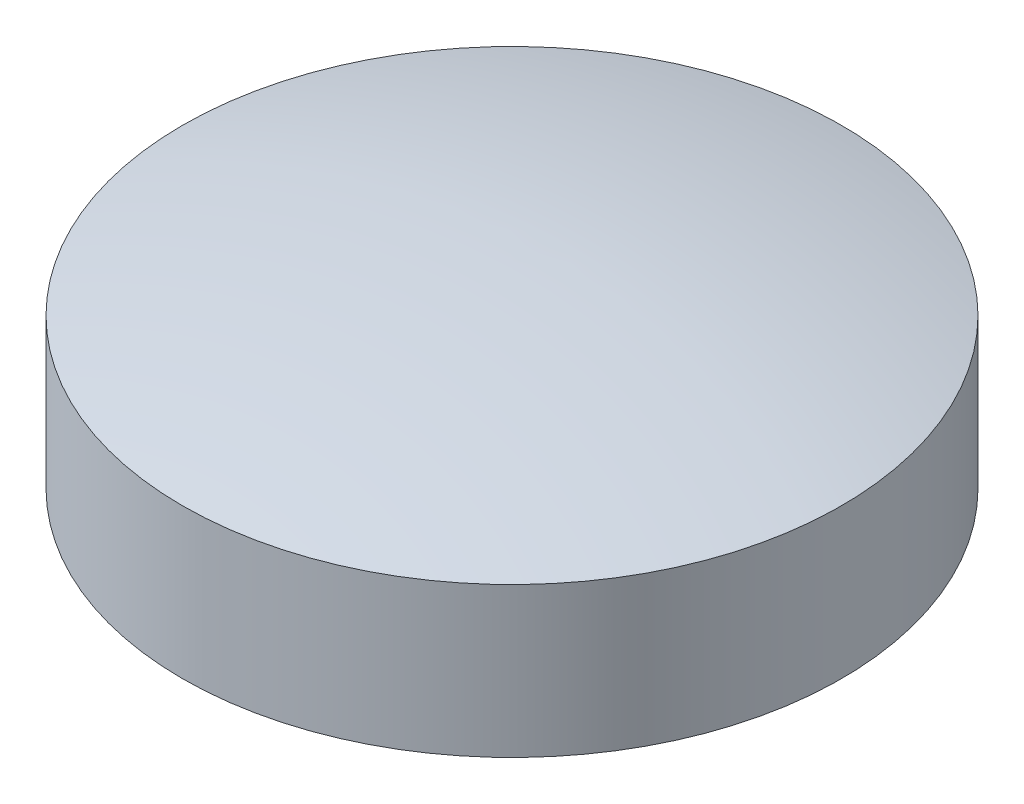
SolidWorks part; units mm, degrees
ref_plane "Front Plane" through (0, 0, 0) normal (0, 0, 1) x (1, 0, 0)
ref_plane "Top Plane" through (0, 0, 0) normal (0, 1, 0) x (1, 0, 0)
ref_plane "Right Plane" through (0, 0, 0) normal (1, 0, 0) x (0, 0, -1)
sketch "Sketch1" plane through (0, 0, 0) normal (0, 0, 1) x (1, 0, 0)
  line L1 (0, 0) -> (-22, 0)
  line L2 (-22, 0) -> (-22, 10)
  line L3 (0, 30) -> (0, -31.2121) construction
  line L4 (0, 13) -> (0, 0)
  arc A0 (-22, 10) -> (0, 13) centre (0, -69.1667) cw
  dimension "D3" = 13
  dimension "D1" = 22
  dimension "D2" = 10
revolve "Revolve1" add sketch "Sketch1" angle 360 about L3
sketch "Sketch2" plane through (0, 0, 0) normal (0, -1, 0) x (1, 0, 0)
  circle A0 centre (-22, 0) radius 1.5
  circle A1 centre (0, 0) radius 22 construction
  dimension "D1" = 3
extrude "Cut-Extrude1" cut sketch "Sketch2" against normal blind 5
